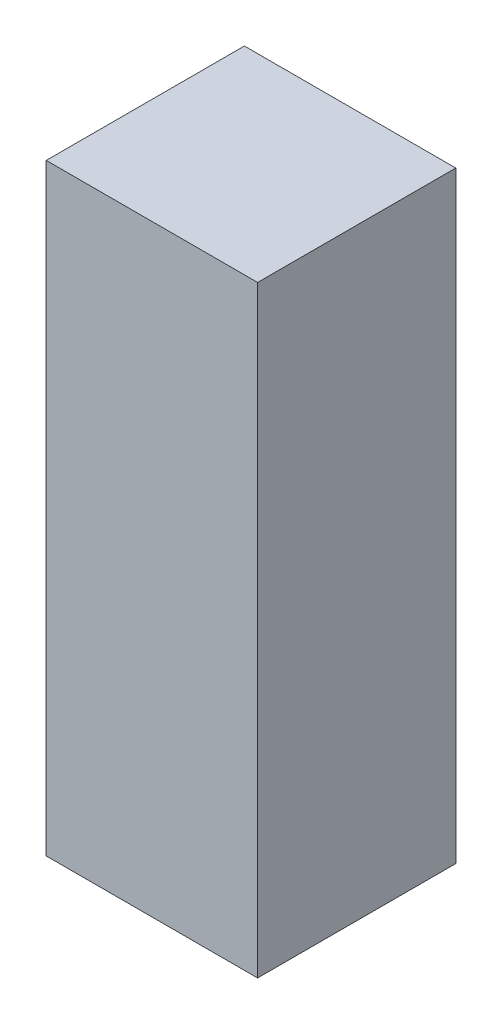
SolidWorks part; units mm, degrees
ref_plane "Front Plane" through (0, 0, 0) normal (0, 0, 1) x (1, 0, 0)
ref_plane "Top Plane" through (0, 0, 0) normal (0, 1, 0) x (1, 0, 0)
ref_plane "Right Plane" through (0, 0, 0) normal (1, 0, 0) x (0, 0, -1)
sketch "Sketch2" plane through (0, 0, 0) normal (0, 1, 0) x (1, 0, 0)
  line L1 (-24, -22.5) -> (24, -22.5)
  line L2 (-24, -22.5) -> (-24, 22.5)
  line L3 (-24, 22.5) -> (24, 22.5)
  line L4 (24, -22.5) -> (24, 22.5)
  line L5 (-24, -22.5) -> (24, 22.5) construction
  line L6 (-24, 22.5) -> (24, -22.5) construction
  point P0 (0, 0)
  dimension "D1" = 45
  dimension "D2" = 48
extrude "Boss-Extrude1" add sketch "Sketch2" along normal blind 136.8
